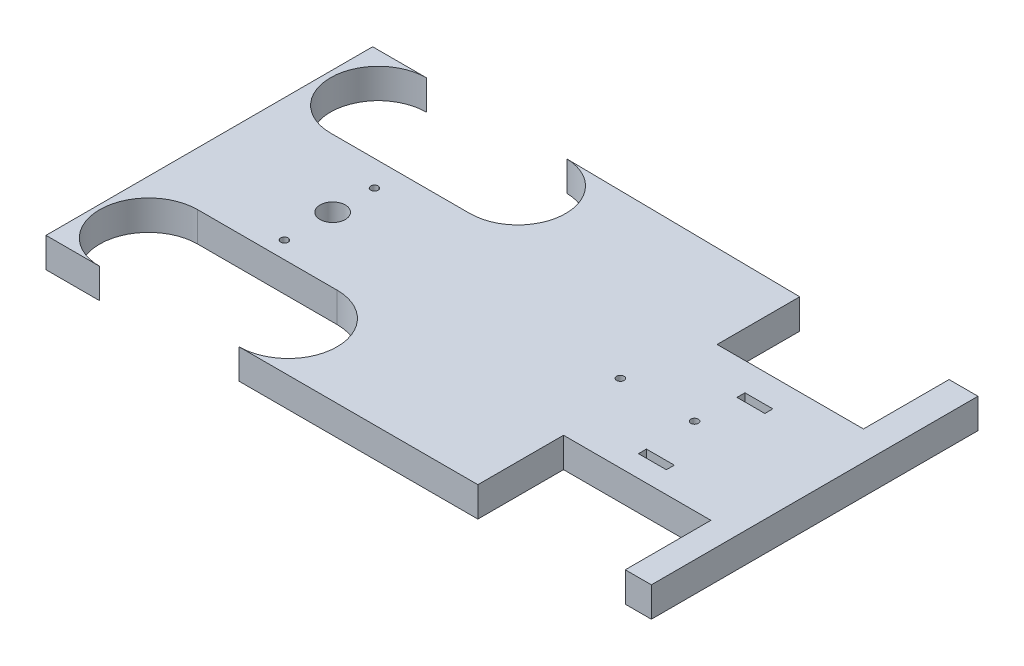
SolidWorks part; units mm, degrees
ref_plane "Front Plane" through (0, 0, 0) normal (0, 0, 1) x (1, 0, 0)
ref_plane "Top Plane" through (0, 0, 0) normal (0, 1, 0) x (1, 0, 0)
ref_plane "Right Plane" through (0, 0, 0) normal (1, 0, 0) x (0, 0, -1)
sketch "Sketch1" plane through (0, 0, 0) normal (0, 1, 0) x (1, 0, 0)
  line L2 (43.4558, 24.4402) -> (43.4558, -19.3652)
  line L4 (-37.7229, 24.4402) -> (-37.7229, -19.3652)
  line L7 (-11.8351, 11.5913) -> (-30.5325, 11.5913)
  line L9 (-11.8351, -6.2119) -> (-30.5325, -6.2119)
  line L13 (39.5766, 24.4402) -> (39.5766, 12.9608)
  line L14 (39.5766, 12.9608) -> (19.9505, 12.9608)
  line L15 (19.9505, 24.0395) -> (19.9505, 12.9608)
  line L16 (39.9592, -7.8796) -> (20.1934, -7.8796)
  line L17 (39.9592, -7.8796) -> (39.9592, -19.3652)
  line L19 (20.1934, -7.8796) -> (20.1934, -19.3652)
  line L20 (-30.5325, -19.3652) -> (-37.7229, -19.3652)
  line L21 (-30.5325, 24.4402) -> (-37.7229, 24.4402)
  line L22 (39.5766, 24.4402) -> (43.4558, 24.4402)
  line L23 (19.9505, 24.0395) -> (-11.8351, 24.4402)
  line L24 (-11.8351, -19.3652) -> (20.1934, -19.3652)
  line L25 (39.9592, -19.3652) -> (43.4558, -19.3652)
  line L26 (31.1689, 9.2152) -> (27.4294, 9.2152)
  line L27 (31.1689, 9.2152) -> (31.1689, 8.1467)
  line L28 (31.1689, 8.1467) -> (27.4294, 8.1467)
  line L29 (27.4294, 9.2152) -> (27.4294, 8.1467)
  line L30 (31.0992, -3.9262) -> (27.3597, -3.9262)
  line L31 (31.0992, -3.9262) -> (31.0992, -4.9946)
  line L32 (31.0992, -4.9946) -> (27.3597, -4.9946)
  line L33 (27.3597, -3.9262) -> (27.3597, -4.9946)
  circle A0 centre (-21.1838, 2.5375) radius 1.6957
  arc A1 (-30.5325, 24.4402) -> (-30.5325, 11.5913) centre (-30.5325, 18.0157) ccw
  arc A2 (-11.8351, 24.4402) -> (-11.8351, 11.5913) centre (-11.8351, 18.0157) cw
  arc A3 (-30.5325, -6.2119) -> (-30.5325, -19.3652) centre (-30.5325, -12.7886) ccw
  arc A4 (-11.8351, -6.2119) -> (-11.8351, -19.3652) centre (-11.8351, -12.7886) cw
  circle A5 centre (27.3597, 2.5375) radius 0.5
  circle A6 centre (17.3979, 2.5375) radius 0.5
  circle A7 centre (-21.1838, 8.1467) radius 0.5
  circle A8 centre (-21.1838, -3.9262) radius 0.5
  point P42 (0, 0)
  dimension "D1" = 1
extrude "Boss-Extrude1" add sketch "Sketch1" along normal blind 4 contours L9 A4 L24 L19 L16 L17 L25 L2 L22 L13 L14 L15 L23 A2 L7 A1 L21 L4 L20 A3 L29 L26 L27 L28 L33 L30 L31 L32 A0
